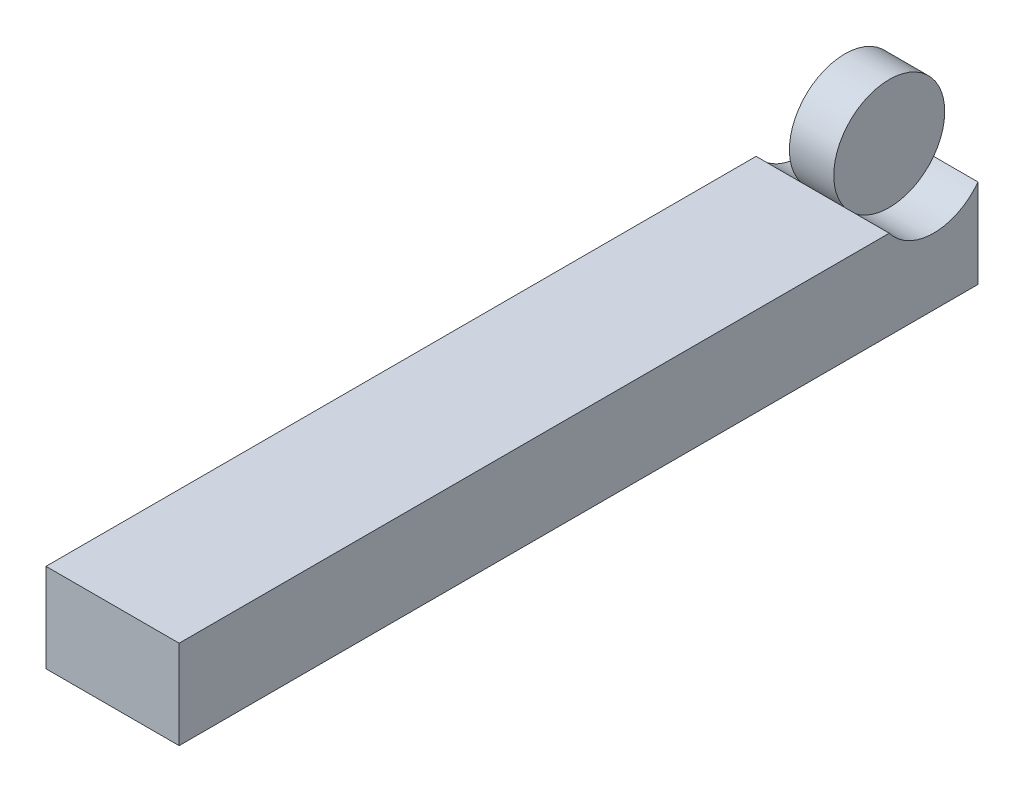
SolidWorks part; units mm, degrees
material "Nylon 101"
ref_plane "Front Plane" through (0, 0, 0) normal (0, 0, 1) x (1, 0, 0)
ref_plane "Top Plane" through (0, 0, 0) normal (0, 1, 0) x (1, 0, 0)
ref_plane "Right Plane" through (0, 0, 0) normal (1, 0, 0) x (0, 0, -1)
sketch "Sketch2" plane through (0, 0, 0) normal (1, 0, 0) x (0, 0, -1)
  line L1 (0, 0) -> (180, 0)
  line L2 (0, 0) -> (0, 20)
  line L3 (0, 20) -> (180, 20)
  line L4 (180, 0) -> (180, 20)
  dimension "D1" = 180
  dimension "D2" = 20
extrude "Boss-Extrude1" add sketch "Sketch2" against normal blind 30
sketch "Sketch3" plane through (0, 0, 0) normal (1, 0, 0) x (0, 0, -1)
  line L1 (180, 20) -> (0, 20) construction
  circle A0 centre (170, 27.5) radius 12.5
  point P6 (160, 20)
  dimension "D1" = 25
  dimension "D2" = 20
extrude "Cut-Extrude2" cut sketch "Sketch3" against normal through all
ref_plane "Plane2" through (-15, 0, 0) normal (1, 0, 0) x (0, 0, -1)
sketch "Sketch5" plane through (-15, 0, 0) normal (1, 0, 0) x (0, 0, -1)
  circle A0 centre (170, 27.5) radius 12.5
  arc A3 (160, 20) -> (180, 20) centre (170, 27.5) ccw construction
  dimension "D1" = 25
extrude "Boss-Extrude4" add sketch "Sketch5" along normal mid plane 10
